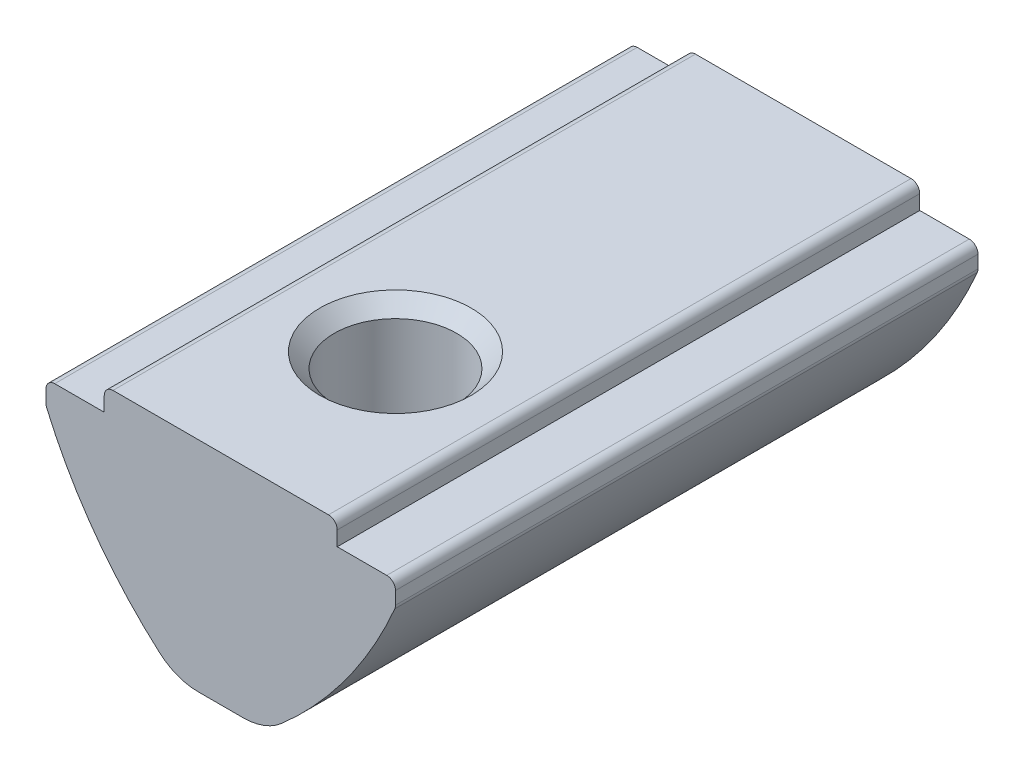
SolidWorks part; units mm, degrees
ref_plane "Спереди" through (0, 0, 0) normal (0, 0, 1) x (1, 0, 0)
ref_plane "Сверху" through (0, 0, 0) normal (0, 1, 0) x (1, 0, 0)
ref_plane "Справа" through (0, 0, 0) normal (1, 0, 0) x (0, 0, -1)
sketch "Эскиз1" plane through (0, 0, 0) normal (0, 0, 1) x (1, 0, 0)
  line L0 (-4, 0) -> (4, 0)
  line L5 (-4, 0) -> (-4, -0.8)
  line L6 (-4, -0.8) -> (-6, -0.8)
  line L7 (-6, -0.8) -> (-6, -1.6)
  line L8 (4, 0) -> (4, -0.8)
  line L9 (4, -0.8) -> (6, -0.8)
  line L10 (6, -0.8) -> (6, -1.6)
  line L11 (-1.5, -7.5) -> (1.5, -7.5)
  arc A0 (-6, -1.6) -> (-1.5, -7.5) centre (7.8062, 4.2641) ccw
  arc A1 (1.5, -7.5) -> (6, -1.6) centre (-7.8062, 4.2641) ccw
  point P0 (0, -7.5)
  point P4 (0, 0)
  dimension "D7" = 15
  dimension "D1" = 8
  dimension "D2" = 12
  dimension "D3" = 0.8
  dimension "D4" = 3
  dimension "D5" = 0.8
  dimension "D6" = 7.5
extrude "Бобышка-Вытянуть1" add sketch "Эскиз1" along normal mid plane 20
fillet "Скругление1" radius 0.3 6 edges at (6, -1.6, 0) (6, -0.8, 0) (-6, -0.8, 0) (-6, -1.6, 0) (4, 0, 0) (-4, 0, 0)
fillet "Скругление2" radius 2 2 edges at (1.5, -7.5, 0) (-1.5, -7.5, 0)
hole_wizard "Отверстие обработанное метчиком M51" positions "Эскиз2" profile "Эскиз4" tap size "M5" standard "ISO" end condition through all
sketch "Эскиз2" plane through (0, 0, 0) normal (0, 1, 0) x (1, 0, 0)
  line L0 (3.7, -10) -> (-3.7, -10) construction
  point P0 (0, -4)
  dimension "D1" = 6
sketch "Эскиз4" plane through (0, 0, 4) normal (1, 0, 0) x (0, 0, 1)
  line L0 (0, 0) -> (0, 7.5)
  line L1 (0, 7.5) -> (2.1, 7.5)
  line L2 (2.1, 7.5) -> (2.1, 0.5)
  line L3 (2.1, 0.5) -> (2.6, 0)
  line L5 (2.6, 0) -> (0, 0)
  line L6 (-2.1, 0.5) -> (-2.6, 0) construction
  line L11 (0, -6.35) -> (0, 107.95) construction
  dimension "Диаметр проходного сверла" = 4.2
  dimension "Глубина проходного сверла" = 7.5
  dimension "Диаметр передней зенковки" = 5.2
  dimension "Угол передней зенковки" = 90
cosmetic thread "Отверстие резьбы1" parameters "D2"=5
sketch "Эскиз5" plane through (0, 0, 0) normal (1, 0, 0) x (0, 0, -1)
  line L1 (6, -4.3) -> (6, -8.3) construction
  line L2 (10, -7.0022) -> (10, -1.657) construction
  line L3 (6, -4.3) -> (6, -8.3)
  line L5 (10, -7.5) -> (-2.0488, -7.5) construction
  arc A0 (6, -4.3) -> (6, -8.3) centre (6, -6.3) ccw
  point P3 (4, -7.4722)
  dimension "D3" = 2
  dimension "D1" = 0.8
  dimension "D2" = 4
revolve "Повернуть1" add sketch "Эскиз5" angle 360 about L1
